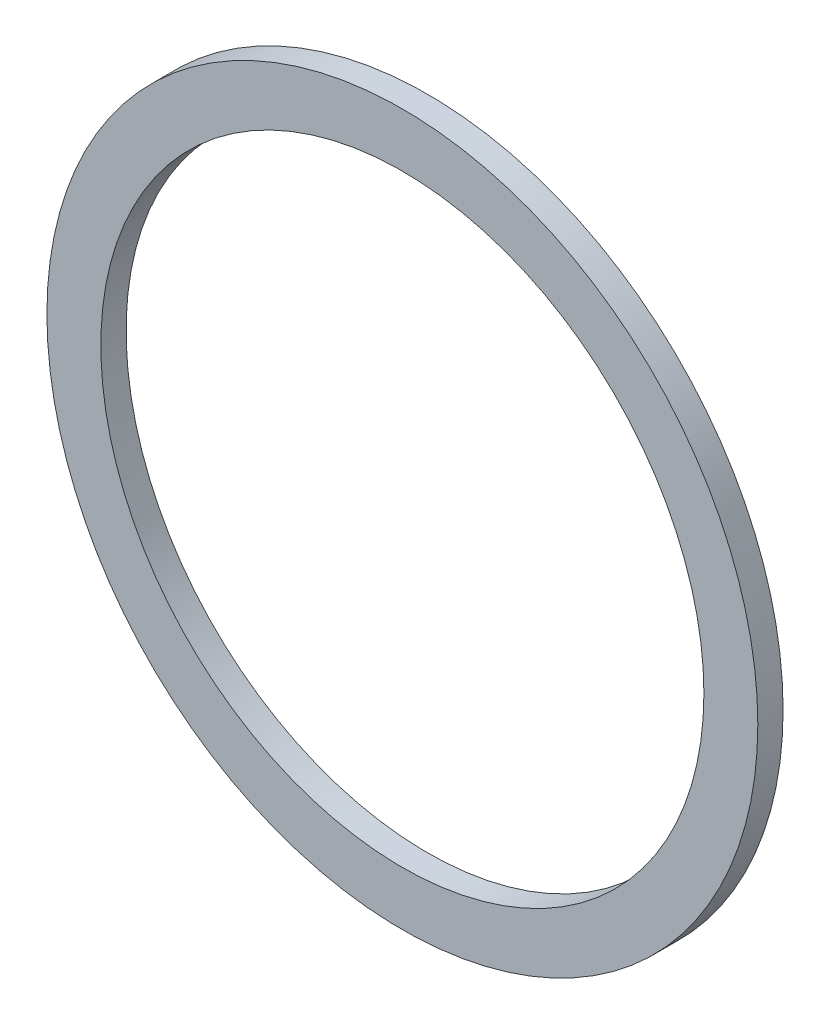
SolidWorks part; units mm, degrees
ref_plane "Front Plane" through (0, 0, 0) normal (0, 0, 1) x (1, 0, 0)
ref_plane "Top Plane" through (0, 0, 0) normal (0, 1, 0) x (1, 0, 0)
ref_plane "Right Plane" through (0, 0, 0) normal (1, 0, 0) x (0, 0, -1)
sketch "Sketch1" plane through (0, 0, 0) normal (0, 0, 1) x (1, 0, 0)
  circle A0 centre (0, 0) radius 10.55
  circle A1 centre (0, 0) radius 8.95
  dimension "D1" = 21.1
  dimension "D2" = 17.9
extrude "Boss-Extrude1" add sketch "Sketch1" along normal blind 0.75
